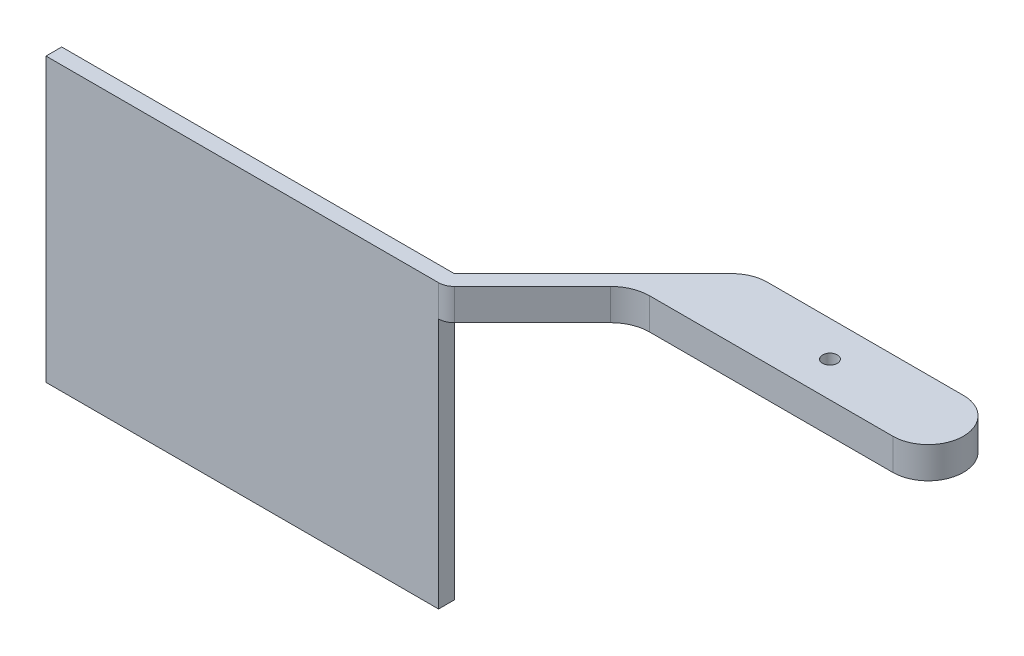
SolidWorks part; units mm, degrees
material "ABS"
ref_plane "Plano frontal" through (0, 0, 0) normal (0, 0, 1) x (1, 0, 0)
ref_plane "Plano superior" through (0, 0, 0) normal (0, 1, 0) x (1, 0, 0)
ref_plane "Plano direito" through (0, 0, 0) normal (1, 0, 0) x (0, 0, -1)
sketch "Esboço1" plane through (0, 0, 0) normal (0, 1, 0) x (1, 0, 0)
  line L0 (-12.5, 0) -> (12.5, 0) construction
  line L1 (-12.5, 4.5) -> (12.5, 4.5)
  line L2 (-12.5, -4.5) -> (12.5, -4.5)
  line L3 (-12.5, 0) -> (-15.682, 3.182) construction
  line L4 (-15.682, 3.182) -> (-33.3597, -14.4957)
  line L5 (-22, -5.9645) -> (-32.5312, -16.4957)
  line L6 (-12.5, -4.5) -> (-18.4645, -4.5)
  line L7 (-83.3597, -16.4957) -> (-32.5312, -16.4957)
  line L9 (-83.3597, -14.4957) -> (-33.3597, -14.4957)
  line L10 (-83.3597, -14.4957) -> (-83.3597, -16.4957)
  line L14 (-33.3597, -14.4957) -> (-33.3597, -16.4957) construction
  arc A0 (-12.5, 4.5) -> (-12.5, -4.5) centre (-12.5, 0) ccw
  arc A1 (12.5, -4.5) -> (12.5, 4.5) centre (12.5, 0) ccw
  arc A3 (-18.4645, -4.5) -> (-22, -5.9645) centre (-18.4645, -9.5) ccw
  point P2 (0, 0)
  dimension "D1" = 4.5
  dimension "D7" = 5
  dimension "D4" = 2
  dimension "D2" = 25
  dimension "D3" = 45
  dimension "D5" = 25
  dimension "D6" = 90
  dimension "D8" = 2
  dimension "D9" = 50
extrude "Ressalto-extrusão1" add sketch "Esboço1" against normal blind 4
sketch "Esboço2" plane through (0, -4, 0) normal (0, -1, 0) x (1, 0, 0)
  line L10 (-33.3597, 14.4957) -> (-83.3597, 14.4957)
  line L11 (-33.3597, 14.4957) -> (-33.3597, 16.4957)
  line L12 (-33.3597, 16.4957) -> (-83.3597, 16.4957)
  line L13 (-83.3597, 14.4957) -> (-83.3597, 16.4957)
extrude "Ressalto-extrusão2" add sketch "Esboço2" along normal blind 32
sketch "Esboço3" plane through (0, 0, 0) normal (0, 1, 0) x (1, 0, 0)
  line L0 (12.5, 0) -> (-12.5, 0) construction
  line L1 (12.5, -4.5) -> (-12.5, -4.5) construction
  line L3 (12.5, 4.5) -> (-12.5, 4.5) construction
  arc A1 (12.5, -4.5) -> (12.5, 4.5) centre (12.5, 0) ccw construction
  circle A3 centre (0, 0) radius 0.94
  arc A4 (12.5, -4.5) -> (12.5, 4.5) centre (12.5, 0) ccw construction
  arc A5 (-12.5, 4.5) -> (-12.5, -4.5) centre (-12.5, 0) ccw construction
  point P8 (0, 0)
  dimension "D7" = 1.88
extrude "Corte-extrusão1" cut sketch "Esboço3" against normal through all
sketch "Esboço6" plane through (0, -4, 0) normal (0, 1, 0) x (1, 0, 0)
  line L0 (-14.05, 0) -> (0, 0) construction
  line L1 (-14.05, 2) -> (-2.2091, 2.65)
  line L2 (-14.05, -2) -> (-2.2091, -2.65)
  line L3 (0, 6.9875) -> (0, -7.5859) construction
  line L4 (14.05, -2) -> (2.2091, -2.65)
  line L5 (14.05, 2) -> (2.2091, 2.65)
  arc A0 (-2.2091, -2.65) -> (2.2091, -2.65) centre (0, 0) ccw
  arc A1 (-14.05, 2) -> (-14.05, -2) centre (-14.05, 0) ccw
  arc A2 (14.05, 2) -> (14.05, -2) centre (14.05, 0) cw
  arc A3 (2.2091, 2.65) -> (-2.2091, 2.65) centre (0, 0) ccw
  dimension "D1" = 4
  dimension "D2" = 6.9
  dimension "D3" = 14.05
  dimension "D4" = 5.3
extrude "Corte-extrusão2" cut sketch "Esboço6" along normal blind 2
fillet "Filete1" radius 2 1 edges at (-32.5312, -2, 16.4957)
